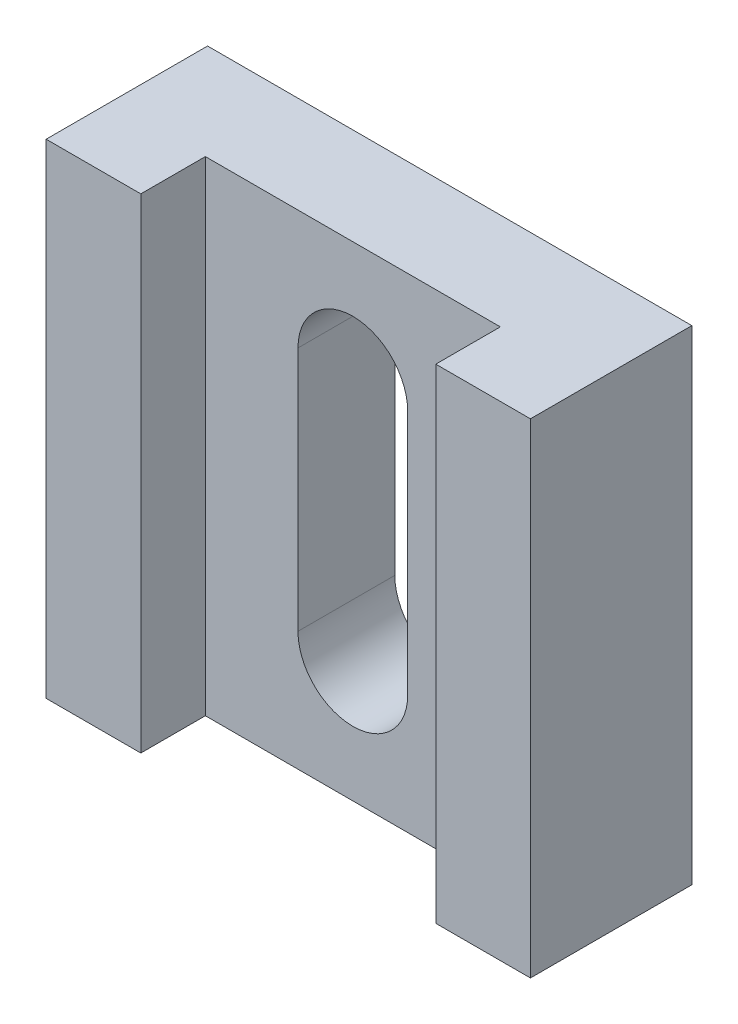
SolidWorks part; units mm, degrees
ref_plane "Front" through (0, 0, 0) normal (0, 0, 1) x (1, 0, 0)
ref_plane "Top" through (0, 0, 0) normal (0, 1, 0) x (1, 0, 0)
ref_plane "Right" through (0, 0, 0) normal (1, 0, 0) x (0, 0, -1)
other "Configuration Table"
sketch "Sketch1" plane through (0, 0, 0) normal (0, 0, 1) x (1, 0, 0)
  line L1 (-7.5, 7.5) -> (7.5, 7.5)
  line L2 (-7.5, 7.5) -> (-7.5, -7.5)
  line L3 (-7.5, -7.5) -> (7.5, -7.5)
  line L4 (7.5, 7.5) -> (7.5, -7.5)
  line L5 (-7.5, 7.5) -> (7.5, -7.5) construction
  line L6 (-7.5, -7.5) -> (7.5, 7.5) construction
  point P0 (0, 0)
extrude "Boss-Extrude1" add sketch "Sketch1" along normal blind 5
sketch "Sketch2" plane through (0, 0, 5) normal (0, 0, 1) x (1, 0, 0)
  line L0 (-7.5, -7.5) -> (7.5, -7.5) construction
  line L1 (-4.5681, 7.5) -> (4.5681, 7.5)
  line L2 (-4.5681, 7.5) -> (-4.5681, -7.5)
  line L3 (-4.5681, -7.5) -> (4.5681, -7.5)
  line L4 (4.5681, 7.5) -> (4.5681, -7.5)
  line L5 (-4.5681, 7.5) -> (4.5681, -7.5) construction
  line L6 (-4.5681, -7.5) -> (4.5681, 7.5) construction
  point P0 (0, 0)
extrude "Cut-Extrude1" cut sketch "Sketch2" against normal blind 2
sketch "Sketch3" plane through (0, 0, 3) normal (0, 0, 1) x (1, 0, 0)
  line L0 (0, 7.5) -> (0, 5.5)
  line L1 (4.5681, 7.5) -> (-4.5681, 7.5) construction
  line L2 (0, -7.5) -> (0, -5.5)
  line L3 (-4.5681, -7.5) -> (4.5681, -7.5) construction
  line L4 (1.7, 3.8) -> (1.7, -3.8)
  line L5 (-1.7, -3.8) -> (-1.7, 3.8)
  circle A0 centre (0, -3.8) radius 1.7
  circle A1 centre (0, 3.8) radius 1.7
extrude "Cut-Extrude2" cut sketch "Sketch3" against normal blind 12 contours A1 | A1 L5 A0 L4 | A0
